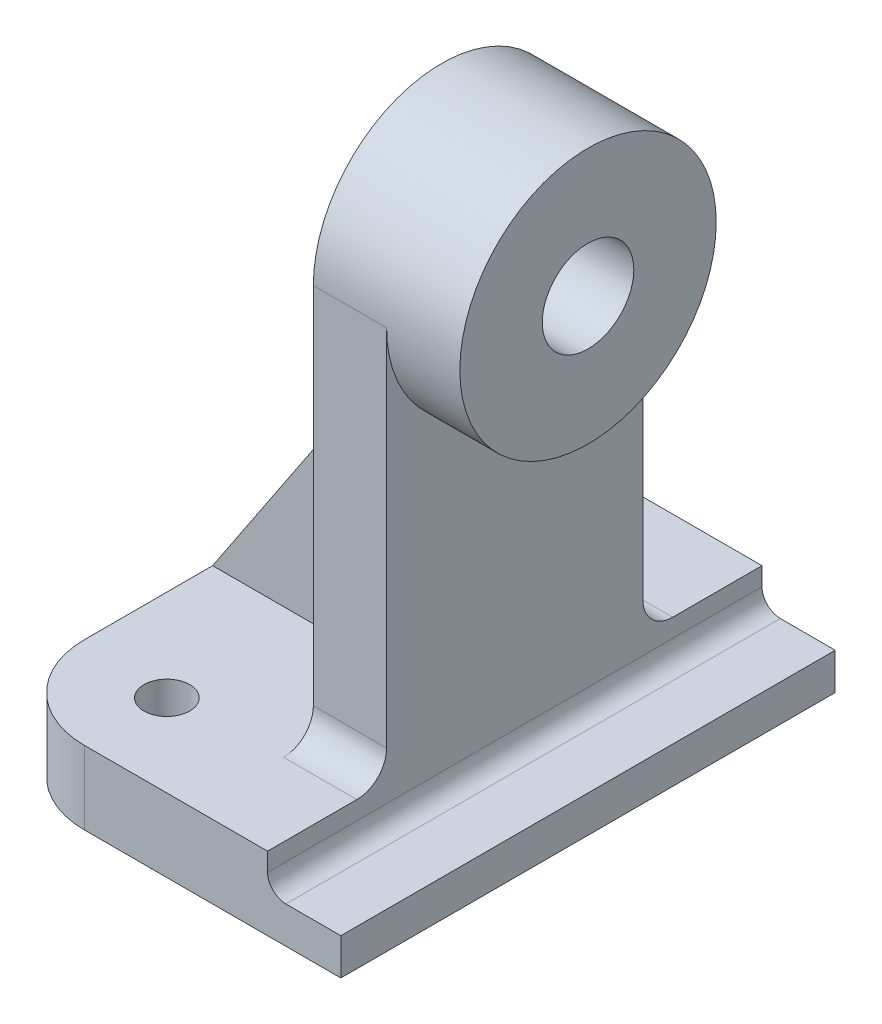
SolidWorks part; units mm, degrees
ref_plane "Ön Düzlem" through (0, 0, 0) normal (0, 0, 1) x (1, 0, 0)
ref_plane "Üst Düzlem" through (0, 0, 0) normal (0, 1, 0) x (1, 0, 0)
ref_plane "Sağ Düzlem" through (0, 0, 0) normal (1, 0, 0) x (0, 0, -1)
sketch "Çizim3" plane through (0, 0, 0) normal (0, 1, 0) x (1, 0, 0)
  line L0 (-19, -17) -> (-19, 17)
  line L1 (-9, 27) -> (19, 27)
  line L2 (19, -27) -> (-9, -27)
  line L3 (19, 27) -> (19, -27)
  arc A0 (-9, 27) -> (-19, 17) centre (-9, 17) ccw
  arc A1 (-9, -27) -> (-19, -17) centre (-9, -17) cw
extrude "Yükseklik-Ekstrüzyon2" add sketch "Çizim3" along normal blind 8
sketch "Çizim4" plane through (0, 8, 0) normal (0, 1, 0) x (1, 0, 0)
  circle A0 centre (-9, -18) radius 2.5
  circle A1 centre (-9, 18) radius 2.5
extrude "Kes-Ekstrüzyon1" cut sketch "Çizim4" against normal blind 8
sketch "Çizim5" plane through (0, 0, 27) normal (0, 0, 1) x (1, 0, 0)
  line L0 (11, 8) -> (19, 8)
  line L1 (19, 8) -> (19, 0) construction
  line L2 (19, 4) -> (13, 4)
  line L3 (11, 6) -> (11, 8)
  line L4 (-9, 8) -> (19, 8) construction
  line L5 (19, 8) -> (19, 4)
  arc A0 (11, 6) -> (13, 4) centre (13, 6) ccw
extrude "Kes-Ekstrüzyon2" cut sketch "Çizim5" against normal blind 54
sketch "Çizim13" plane through (0, 8, 0) normal (0, 1, 0) x (1, 0, 0)
  line L1 (11, 27) -> (11, -27) construction
  line L5 (11, 20.5) -> (11, -20.5)
  line L7 (3, 20.5) -> (3, -20.5)
  line L8 (3, 20.5) -> (11, 20.5)
  line L9 (3, -20.5) -> (11, -20.5)
extrude "Yükseklik-Ekstrüzyon8" add sketch "Çizim13" along normal blind 43
sketch "Çizim14" plane through (3, 0, 0) normal (-1, 0, 0) x (0, 0, 1)
  line L0 (20.5, 8) -> (20.5, 51)
  line L2 (17.25, 8) -> (20.5, 8)
  line L3 (14, 11.25) -> (14, 51)
  line L4 (-20.5, 51) -> (20.5, 51) construction
  line L5 (20.5, 51) -> (14, 51)
  line L7 (-20.5, 51) -> (-14, 51)
  line L8 (-14, 11.25) -> (-14, 51)
  line L9 (-17.25, 8) -> (-20.5, 8)
  line L10 (-20.5, 8) -> (-20.5, 51)
  arc A0 (14, 11.25) -> (17.25, 8) centre (17.25, 11.25) ccw
  arc A1 (-14, 11.25) -> (-17.25, 8) centre (-17.25, 11.25) cw
extrude "Kes-Ekstrüzyon7" cut sketch "Çizim14" against normal blind 43
sketch "Çizim15" plane through (11, 0, 0) normal (1, 0, 0) x (0, 0, -1)
  line L0 (-14, 51) -> (14, 51) construction
  circle A0 centre (0, 51) radius 14
extrude "Yükseklik-Ekstrüzyon9" add sketch "Çizim15" along normal blind 8 and the other way blind 8
sketch "Çizim16" plane through (19, 0, 0) normal (1, 0, 0) x (0, 0, -1)
  circle A0 centre (0, 51) radius 5
extrude "Kes-Ekstrüzyon8" cut sketch "Çizim16" against normal blind 16
ref_plane "Düzlem2" through (0, 0, 0) normal (0, 0, 1) x (1, 0, 0)
sketch "Çizim17" plane through (0, 0, 0) normal (0, 0, 1) x (1, 0, 0)
  line L0 (-19, 8) -> (3, 41)
  line L1 (3, 51) -> (3, 11.25) construction
rib "Feder12" sketch "Çizim17" sketch "Çizim17" thickness 6 extrusion direction parallel to sketch draft on no parameters "D1"=6
